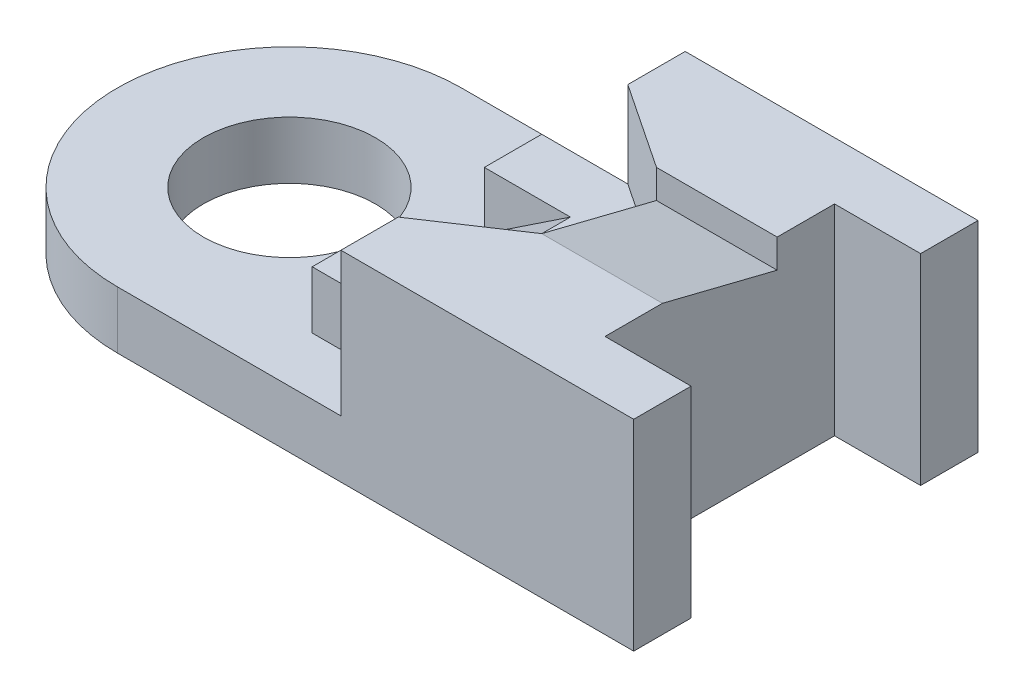
SolidWorks part; units mm, degrees
ref_plane "Front" through (0, 0, 0) normal (0, 0, 1) x (1, 0, 0)
ref_plane "Top" through (0, 0, 0) normal (0, 1, 0) x (1, 0, 0)
ref_plane "Right" through (0, 0, 0) normal (1, 0, 0) x (0, 0, -1)
sketch "Sketch1" plane through (0, 0, 0) normal (0, 1, 0) x (1, 0, 0)
  line L0 (9, 4) -> (9, 6)
  line L1 (-9, -6) -> (9, -6)
  line L3 (-9, 6) -> (9, 6)
  line L4 (9, -6) -> (9, -4)
  line L5 (-9, -6) -> (9, 6) construction
  line L6 (-9, 6) -> (9, -6) construction
  line L7 (9, 4) -> (6, 4)
  line L9 (9, -4) -> (6, -4)
  line L10 (6, 4) -> (6, -4)
  circle A0 centre (-9, 0) radius 3
  arc A1 (-9, 6) -> (-9, -6) centre (-9, 0) ccw
  point P0 (0, 0)
  dimension "D3" = 6
  dimension "D1" = 18
  dimension "D2" = 12
  dimension "D4" = 2
  dimension "D5" = 2
  dimension "D6" = 3
extrude "Boss-Extrude1" add sketch "Sketch1" along normal blind 2
sketch "Sketch2" plane through (0, 2, 0) normal (0, 1, 0) x (1, 0, 0)
  line L0 (9, 6) -> (-1.2057, 6)
  line L1 (9, 6) -> (-9, 6) construction
  line L2 (-1.2057, 6) -> (-1.2057, 4)
  line L3 (-1.2057, 4) -> (-4.2057, 4)
  line L4 (-4.2057, 4) -> (-4.2057, -4)
  line L5 (-4.2057, -4) -> (-1.2057, -4)
  line L6 (-1.2057, -4) -> (-1.2057, -6)
  line L7 (-9, -6) -> (9, -6) construction
  line L8 (-1.2057, -6) -> (9, -6)
  line L9 (9, -6) -> (9, -4)
  line L10 (9, -4) -> (6, -4)
  line L11 (6, -4) -> (6, 4)
  line L12 (6, 4) -> (9, 4)
  line L13 (9, 4) -> (9, 6)
  dimension "D1" = 2
  dimension "D2" = 3
  dimension "D3" = 3
  dimension "D4" = 2
extrude "Boss-Extrude2" add sketch "Sketch2" along normal blind 2
sketch "Sketch3" plane through (0, 0, 0) normal (0, 0, 1) x (1, 0, 0)
  line L0 (-1.2057, 4) -> (-4.2057, 2)
  line L1 (-4.2057, 2) -> (-4.2057, 4)
  line L2 (-4.2057, 4) -> (-1.2057, 4)
extrude "Cut-Extrude1" cut sketch "Sketch3" against normal mid plane 4
sketch "Sketch4" plane through (0, 4, 0) normal (0, 1, 0) x (1, 0, 0)
  line L0 (9, 6) -> (-1.2057, 6)
  line L1 (-1.2057, 6) -> (-1.2057, 4)
  line L2 (-1.2057, 4) -> (1.7943, 2)
  line L3 (1.7943, 2) -> (1.7943, -2)
  line L4 (1.7943, -2) -> (-1.2057, -4)
  line L5 (-1.2057, -4) -> (-1.2057, -6)
  line L6 (-1.2057, -6) -> (9, -6)
  line L7 (9, -6) -> (9, -4)
  line L8 (9, -4) -> (6, -4)
  line L9 (6, -4) -> (6, 4)
  line L10 (6, 4) -> (9, 4)
  line L11 (9, 4) -> (9, 6)
  dimension "D1" = 3
  dimension "D2" = 2
  dimension "D3" = 2
extrude "Boss-Extrude3" add sketch "Sketch4" along normal blind 3
sketch "Sketch5" plane through (6, 0, 0) normal (1, 0, 0) x (0, 0, -1)
  line L0 (2, 7) -> (2, 6)
  line L1 (2, 7) -> (2, 4) construction
  line L2 (2, 6) -> (-2, 7)
  line L3 (-2, 7) -> (2, 7)
  dimension "D1" = 1
extrude "Cut-Extrude2" cut sketch "Sketch5" against normal blind 13
